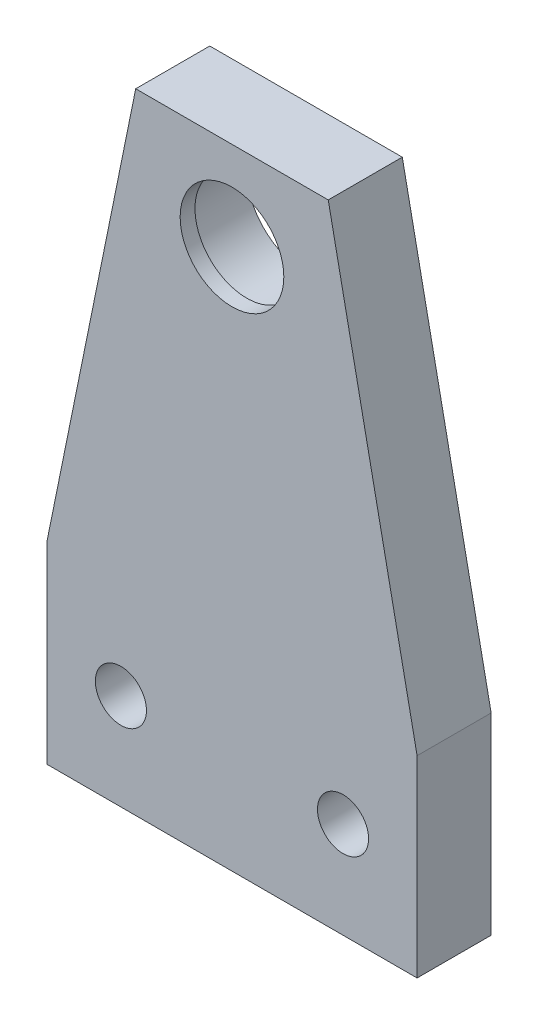
SolidWorks part; units mm, degrees
material "ABS"
ref_plane "前视基准面" through (0, 0, 0) normal (0, 0, 1) x (1, 0, 0)
ref_plane "上视基准面" through (0, 0, 0) normal (0, 1, 0) x (1, 0, 0)
ref_plane "右视基准面" through (0, 0, 0) normal (1, 0, 0) x (0, 0, -1)
sketch "草图1" plane through (0, 0, 0) normal (0, 0, 1) x (1, 0, 0)
  line L0 (-25, 0) -> (25, 0)
  line L1 (25, 0) -> (25, 26)
  line L4 (13, 85) -> (-13, 85)
  line L7 (-25, 26) -> (-25, 0)
  line L8 (0, -30.1401) -> (0, 136.3287) construction
  line L9 (-91.0979, 13) -> (78.0415, 13) construction
  line L10 (13, 85) -> (25, 26)
  line L11 (-13, 85) -> (-25, 26)
  circle A0 centre (0, 73) radius 7
  circle A3 centre (-15, 13) radius 3.45
  circle A6 centre (15, 13) radius 3.45
  dimension "D5" = 6.9
  dimension "D6" = 12
  dimension "D8" = 10
  dimension "D9" = 14
  dimension "D1" = 50
  dimension "D2" = 85
  dimension "D3" = 26
  dimension "D4" = 26
extrude "凸台-拉伸1" add sketch "草图1" along normal blind 10
sketch "草图2" plane through (0, 0, 0) normal (0, 0, -1) x (-1, 0, 0)
  circle A0 centre (0, 73) radius 4
  circle A1 centre (0, 73) radius 8.05
  dimension "D1" = 8
  dimension "D2" = 16.1
extrude "切除-拉伸1" cut sketch "草图2" against normal blind 8
